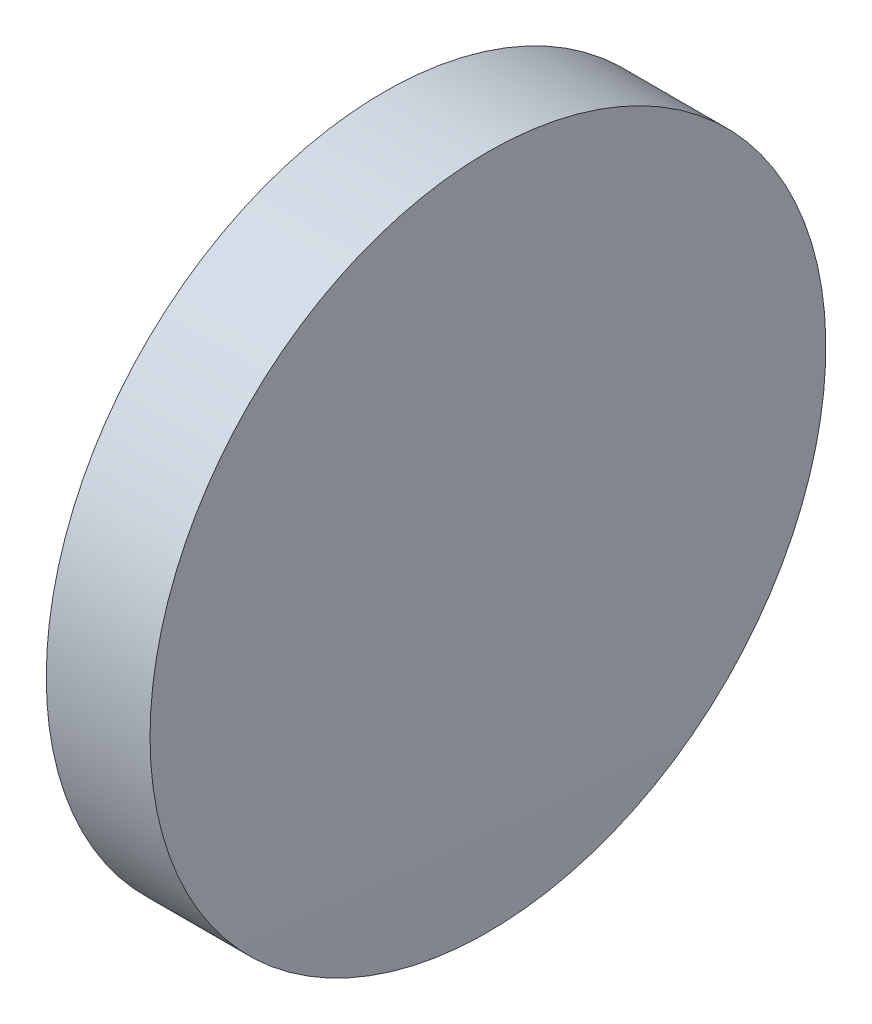
SolidWorks part; units mm, degrees
ref_plane "前视基准面" through (0, 0, 0) normal (0, 0, 1) x (1, 0, 0)
ref_plane "上视基准面" through (0, 0, 0) normal (0, 1, 0) x (1, 0, 0)
ref_plane "右视基准面" through (0, 0, 0) normal (1, 0, 0) x (0, 0, -1)
sketch "草图1" plane through (0, 0, 0) normal (0, 0, 1) x (1, 0, 0)
  line L0 (110.1654, 65.2336) -> (128.9614, 65.2336) construction
  line L1 (115.7646, 65.2336) -> (115.7646, 77.9336)
  line L2 (119.7646, 65.2336) -> (115.7646, 65.2336)
  line L5 (115.7646, 77.9336) -> (119.6646, 77.9336)
  arc A0 (119.7646, 65.2336) -> (119.6646, 77.9336) centre (-686.7354, 65.2336) ccw
revolve "旋转1" add sketch "草图1" angle 360 about L0
